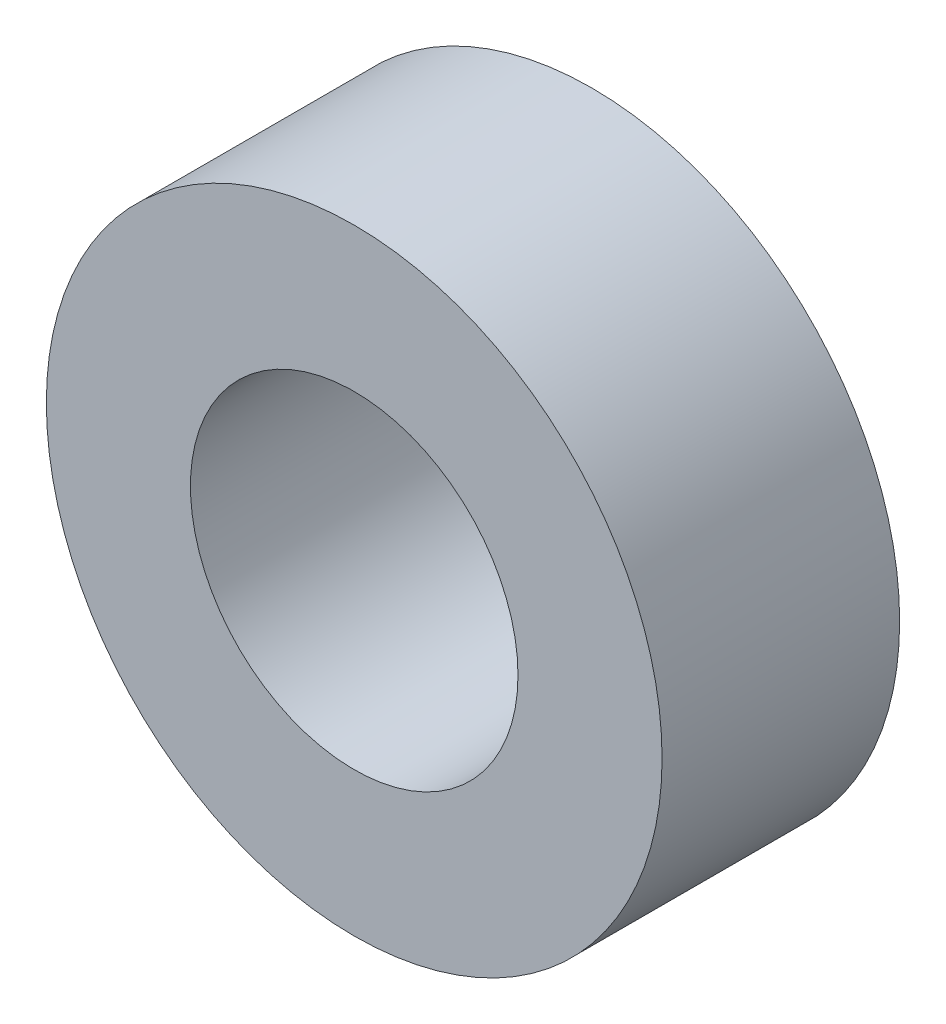
SolidWorks part; units mm, degrees
ref_plane "Front Plane" through (0, 0, 0) normal (0, 0, 1) x (1, 0, 0)
ref_plane "Top Plane" through (0, 0, 0) normal (0, 1, 0) x (1, 0, 0)
ref_plane "Right Plane" through (0, 0, 0) normal (1, 0, 0) x (0, 0, -1)
sketch "Sketch1" plane through (0, 0, 0) normal (0, 0, 1) x (1, 0, 0)
  circle A0 centre (0, 0) radius 6.35
  circle A1 centre (0, 0) radius 3.3782
  dimension "D1" = 12.7
  dimension "D2" = 6.7564
extrude "Boss-Extrude1" add sketch "Sketch1" along normal blind 4.9
